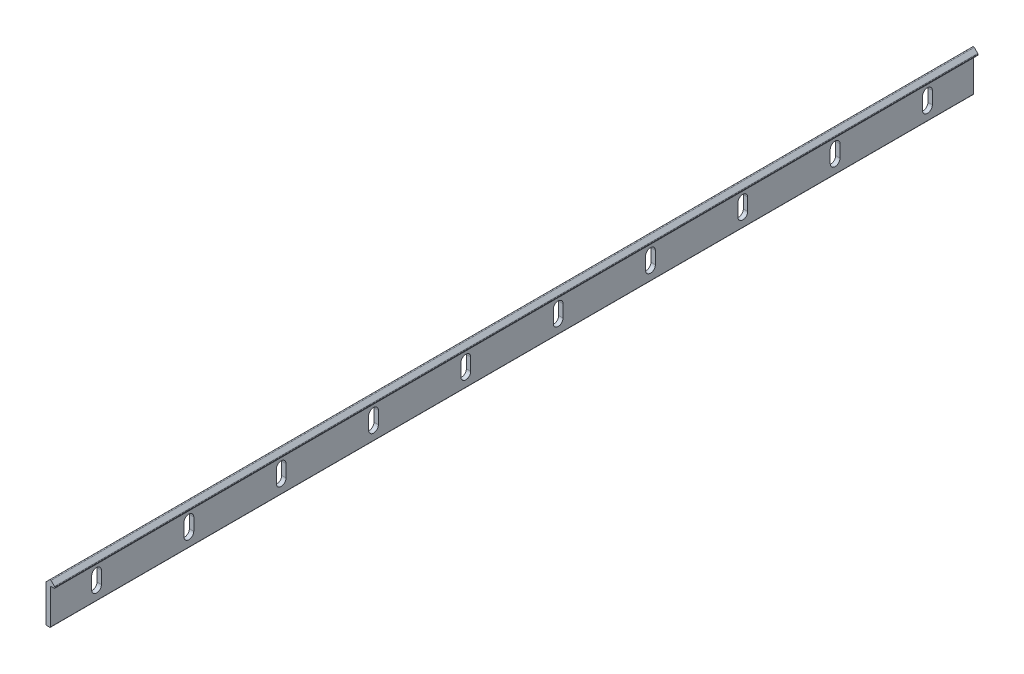
SolidWorks part; units mm, degrees
material "6061-T6 (SS)"
ref_plane "Front Plane" through (0, 0, 0) normal (0, 0, 1) x (1, 0, 0)
ref_plane "Top Plane" through (0, 0, 0) normal (0, 1, 0) x (1, 0, 0)
ref_plane "Right Plane" through (0, 0, 0) normal (1, 0, 0) x (0, 0, -1)
sketch "Sketch1" plane through (0, 0, 0) normal (0, 0, 1) x (1, 0, 0)
  line L0 (0, 20.3302) -> (2.0196, 22.3498)
  line L1 (0, 0) -> (2.375, 0)
  line L2 (0, 20.3302) -> (0, 0)
  line L4 (2.375, 0) -> (2.375, 19.5291)
  line L5 (2.375, 19.5291) -> (4.75, 19.5291)
  line L7 (2.7304, 22.3498) -> (4.75, 20.3302)
  line L8 (4.75, 19.5291) -> (4.75, 20.3302)
  arc A0 (2.7304, 22.3498) -> (2.0196, 22.3498) centre (2.375, 21.9944) ccw
  point P9 (2.375, 22.7052)
  dimension "D5" = 0.5026
  dimension "D6" = 22.497
  dimension "D1" = 2.375
  dimension "D2" = 19.5291
  dimension "D3" = 2.375
  dimension "D4" = 2.9679
extrude "Boss-Extrude1" add sketch "Sketch1" along normal blind 500
fillet "Fillet1" radius 0.5033 1 edges at (0, 20.3302, 250)
fillet "Fillet2" radius 0.504 1 edges at (4.75, 20.3302, 250)
fillet "Fillet3" radius 0.3016 1 edges at (4.75, 19.5291, 250)
fillet "Fillet4" radius 0.3016 2 edges at (0, 0, 250) (2.375, 0, 250)
sketch "Sketch2" plane through (0, 0, 0) normal (-1, 0, 0) x (0, 0, 1)
  line L0 (25, 13.1043) -> (25, 6.4043) construction
  line L1 (27.65, 13.1043) -> (27.65, 6.4043)
  line L2 (22.35, 13.1043) -> (22.35, 6.4043)
  line L3 (500, 0) -> (0, 0) construction
  line L4 (0, 20.1217) -> (0, 0.3016) construction
  arc A0 (27.65, 13.1043) -> (22.35, 13.1043) centre (25, 13.1043) ccw
  arc A1 (22.35, 6.4043) -> (27.65, 6.4043) centre (25, 6.4043) ccw
  point P2 (25, 9.7543)
  dimension "D3" = 9.7543
  dimension "D1" = 5.3
  dimension "D2" = 6.7
  dimension "D4" = 25
extrude "Cut-Extrude1" cut sketch "Sketch2" against normal up to next (2.375 mm away)
pattern_linear "LPattern1" count 10 spacing 50 along (0, 0, 1) of "Cut-Extrude1"
ref_plane "Inside Face" through (1.1875, 0, 0) normal (1, 0, 0) x (0, 0, -1)
equation "\"D3@Sketch1\"=\"D1@Sketch1\""
